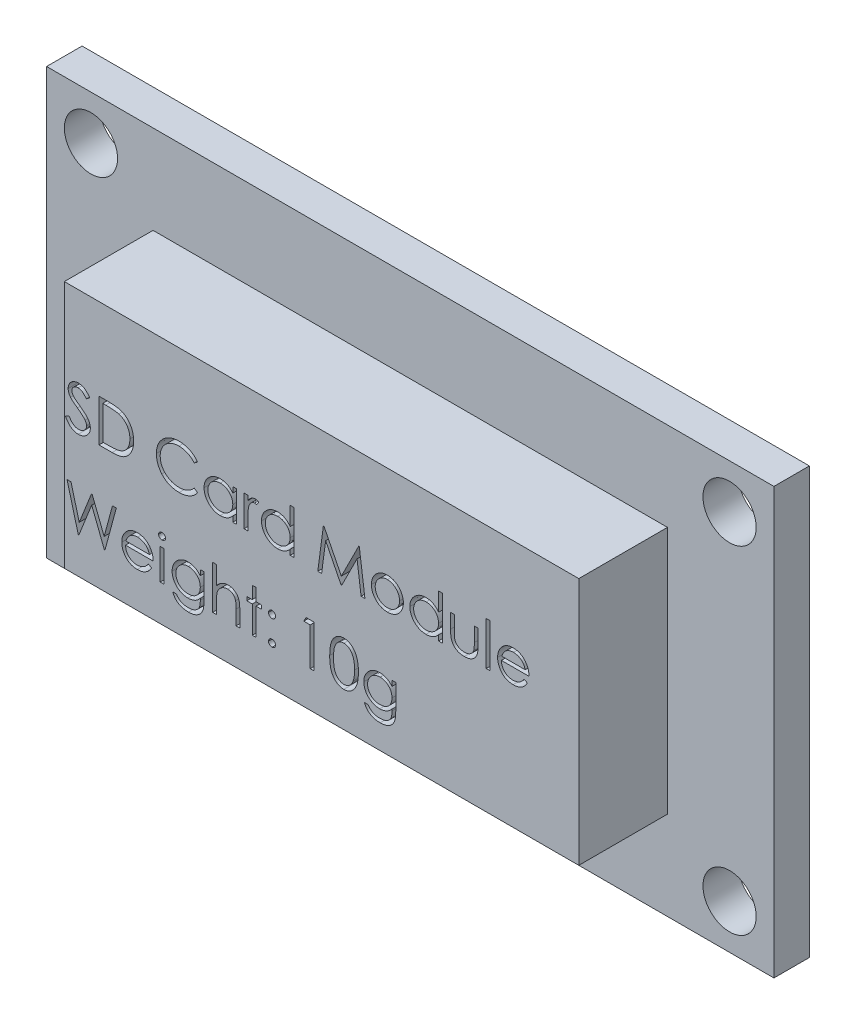
SolidWorks part; units mm, degrees
ref_plane "Front Plane" through (0, 0, 0) normal (0, 0, 1) x (1, 0, 0)
ref_plane "Top Plane" through (0, 0, 0) normal (0, 1, 0) x (1, 0, 0)
ref_plane "Right Plane" through (0, 0, 0) normal (1, 0, 0) x (0, 0, -1)
sketch "Sketch1" plane through (0, 0, 0) normal (0, 0, 1) x (1, 0, 0)
  line L0 (-20.5, -12) -> (20.5, -12)
  line L1 (-20.5, -12) -> (-20.5, 12)
  line L2 (-20.5, 12) -> (20.5, 12)
  line L3 (20.5, -12) -> (20.5, 12)
  line L4 (0, 12) -> (0, -12) construction
  line L5 (-20.5, 0) -> (20.5, 0) construction
  line L6 (-18, -9.5) -> (18, -9.5)
  line L7 (-18, -9.5) -> (-18, 9.5)
  line L8 (-18, 9.5) -> (18, 9.5)
  line L9 (18, -9.5) -> (18, 9.5)
  line L10 (-18, -9.5) -> (18, 9.5) construction
  line L11 (-18, 9.5) -> (18, -9.5) construction
  circle A0 centre (-18, 9.5) radius 1.4993
  circle A1 centre (-18, -9.5) radius 1.5
  circle A2 centre (18, -9.5) radius 1.5
  circle A3 centre (18, 9.5) radius 1.5
  point P4 (0, 0)
  point P17 (0, 0)
  dimension "D5" = 2.9987
  dimension "D6" = 3
  dimension "D7" = 3
  dimension "D8" = 3
  dimension "D1" = 24
  dimension "D2" = 41
  dimension "D3" = 2.5
  dimension "D4" = 2.5
extrude "Boss-Extrude1" add sketch "Sketch1" along normal blind 2 contours L0 L3 L2 L1 A3 L9 A2 L6 A1 L7 A0 L8 | A3 L8 A0 L7 A1 L6 A2 L9
sketch "Sketch2" plane through (0, 0, 2) normal (0, 0, 1) x (1, 0, 0)
  line L0 (-20.5, 12) -> (20.5, 12) construction
  line L1 (-14.5, -7) -> (14.5, -7)
  line L2 (-14.5, -7) -> (-14.5, 7)
  line L3 (-14.5, 7) -> (14.5, 7)
  line L4 (14.5, -7) -> (14.5, 7)
  line L5 (-14.5, -7) -> (14.5, 7) construction
  line L6 (-14.5, 7) -> (14.5, -7) construction
  line L7 (-20.5, -12) -> (-20.5, 12) construction
  point P0 (0, 0)
  dimension "D1" = 5
  dimension "D2" = 6
extrude "Boss-Extrude2" add sketch "Sketch2" along normal blind 5
sketch "Sketch3" plane through (0, 0, 7) normal (0, 0, 1) x (1, 0, 0)
  line L0 (-14.5, 0) -> (14.5, 0) construction
  line L1 (-14.5, 7) -> (-14.5, -7) construction
  line L2 (14.5, -7) -> (14.5, 7) construction
  line L3 (-14.5, 7) -> (-14.5, -7) construction
  text T0 "SD Card Module\r\nWeight: 10g" font "Century Gothic" height in points 9
  dimension "D1" = 14.5
  dimension "D2" = 14.5
extrude "Cut-Extrude1" cut sketch "Sketch3" against normal blind 2
